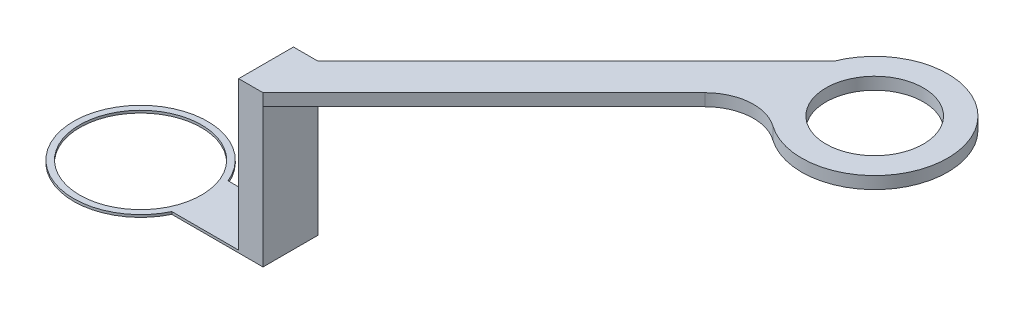
SolidWorks part; units mm, degrees
ref_plane "Alzado" through (0, 0, 0) normal (0, 0, 1) x (1, 0, 0)
ref_plane "Planta" through (0, 0, 0) normal (0, 1, 0) x (1, 0, 0)
ref_plane "Vista lateral" through (0, 0, 0) normal (1, 0, 0) x (0, 0, -1)
sketch "Croquis1" plane through (0, 0, 0) normal (0, 1, 0) x (1, 0, 0)
  line L2 (5.0782, 2.1123) -> (12.4433, 2.1123)
  line L3 (12.4433, 2.1123) -> (12.4433, -2.3877)
  line L4 (12.4433, -2.3877) -> (4.9547, -2.3877)
  circle A0 centre (0, 0) radius 5
  arc A1 (5.0782, 2.1123) -> (4.9547, -2.3877) centre (0, 0) ccw
  point P8 (0, 0)
extrude "Saliente-Extruir2" add sketch "Croquis1" along normal blind 0.2
sketch "Croquis2" plane through (0, 0.2, 0) normal (0, 1, 0) x (1, 0, 0)
  line L0 (4.9547, -2.3877) -> (12.4433, -2.3877) construction
  line L1 (12.4433, 2.1123) -> (10.4433, 2.1123)
  line L2 (12.4433, 2.1123) -> (12.4433, -2.3877)
  line L3 (12.4433, -2.3877) -> (10.4433, -2.3877)
  line L4 (10.4433, 2.1123) -> (10.4433, -2.3877)
extrude "Saliente-Extruir3" add sketch "Croquis2" along normal blind 12.2
sketch "Croquis4" plane through (0, 12.4, 0) normal (0, 1, 0) x (1, 0, 0)
  line L0 (10.4433, -2.3877) -> (17.2719, 4.4409)
  line L1 (17.2719, 4.4409) -> (12.8245, -0.0064)
  line L2 (10.4433, -2.3877) -> (19.454, -2.3877) construction
  dimension "D1" = 45
sketch "Croquis7" plane through (12.4433, 0, 0) normal (1, 0, 0) x (0, 0, -1)
  line L1 (2.1123, 12.4) -> (2.1123, 0) construction
  line L2 (-2.3877, 12.4) -> (2.1123, 12.4)
  line L3 (-2.3877, 12.4) -> (-2.3877, 11.4)
  line L4 (-2.3877, 11.4) -> (2.1123, 11.4)
  line L5 (2.1123, 12.4) -> (2.1123, 11.4)
extrude "Saliente-Extruir6" add sketch "Croquis7" along direction (0.7071, 0, -0.7071) on the side of the normal blind 30
sketch "Croquis9" plane through (0, 12.4, 0) normal (0, 1, 0) x (1, 0, 0)
  line L0 (33.6565, 23.3255) -> (33.6565, 18.8255)
  arc A0 (33.6565, 18.8255) -> (33.6565, 23.3255) centre (39.2187, 21.0755) ccw
  circle A1 centre (39.2187, 21.0755) radius 4
extrude "Saliente-Extruir7" add sketch "Croquis9" against normal up to surface (1 mm away) up to face at (28.3532, 11.4, -15.2097)
fillet "Redondeo1" radius 4 1 edges at (33.6565, 11.9, -18.8255)
